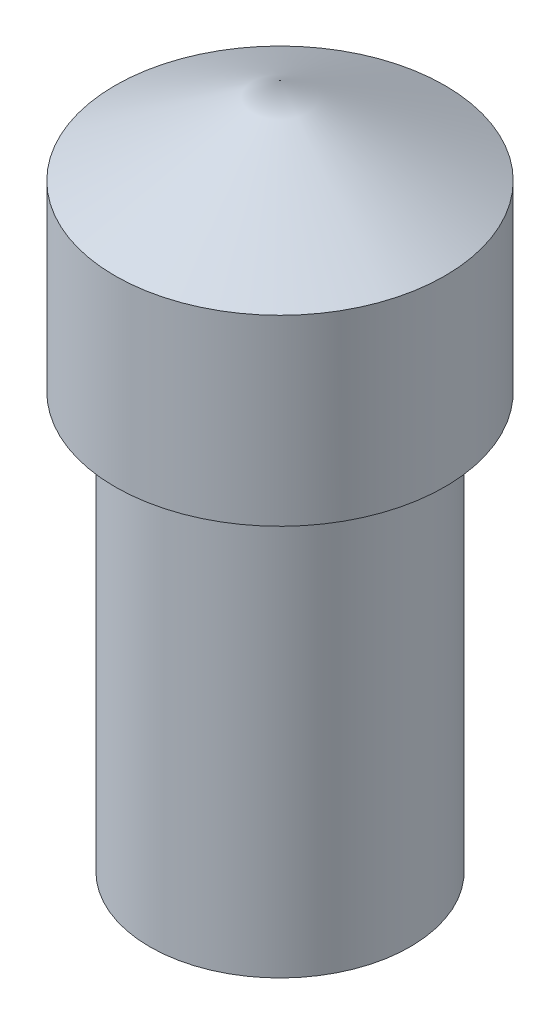
SolidWorks part; units mm, degrees
material "Stainless Steel (ferritic)"
ref_plane "Front Plane" through (0, 0, 0) normal (0, 0, 1) x (1, 0, 0)
ref_plane "Top Plane" through (0, 0, 0) normal (0, 1, 0) x (1, 0, 0)
ref_plane "Right Plane" through (0, 0, 0) normal (1, 0, 0) x (0, 0, -1)
sketch "Sketch2" plane through (0, 0, 0) normal (0, 0, 1) x (1, 0, 0)
  line L0 (0, 0) -> (0.75, 0)
  line L1 (0.75, 0) -> (0.75, 2.3947)
  line L2 (0.75, 2.3947) -> (0.95, 2.3947)
  line L3 (0.95, 2.3947) -> (0.95, 3.4474)
  line L4 (0.95, 3.4474) -> (0, 3.9474)
  line L5 (0, 3.9474) -> (0, 0)
  dimension "D1" = 0.75
  dimension "D2" = 0.2
revolve "Revolve1" add sketch "Sketch2" angle 360 about L5
